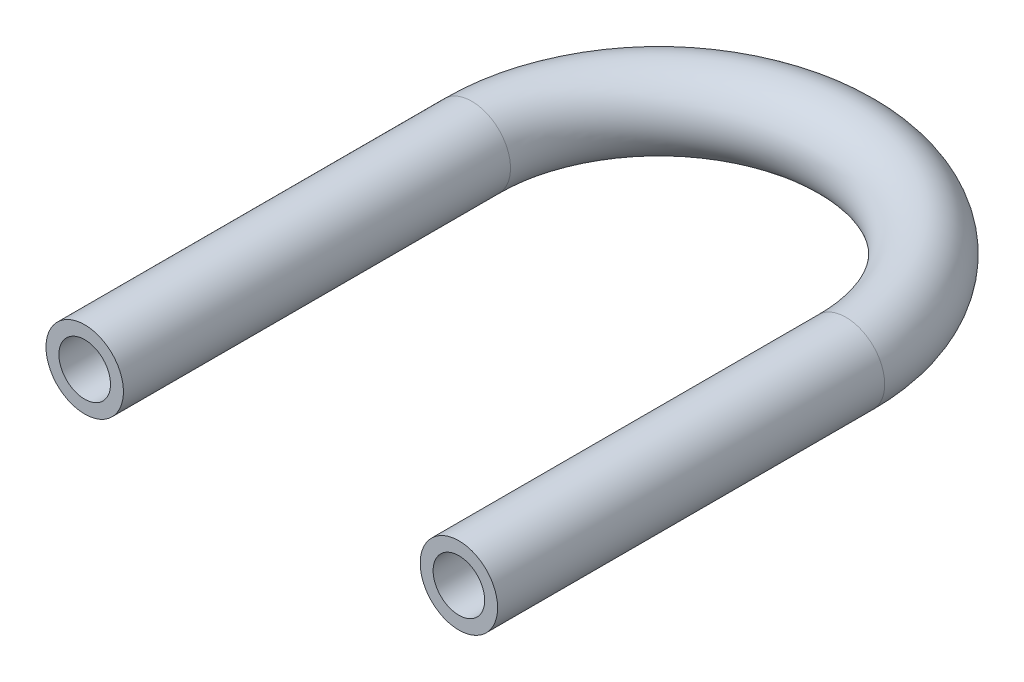
SolidWorks part; units mm, degrees
ref_plane "Front Plane" through (0, 0, 0) normal (0, 0, 1) x (1, 0, 0)
ref_plane "Top Plane" through (0, 0, 0) normal (0, 1, 0) x (1, 0, 0)
ref_plane "Right Plane" through (0, 0, 0) normal (1, 0, 0) x (0, 0, -1)
sketch "Sketch1" plane through (0, 0, 0) normal (0, 1, 0) x (1, 0, 0)
  line L0 (-14.5, 0) -> (-14.5, -30)
  line L1 (14.5, 0) -> (14.5, -30)
  arc A0 (-14.5, 0) -> (14.5, 0) centre (0, 0) cw
  dimension "D1" = 14.5
  dimension "D2" = 30
ref_plane "Plane1" through (-14.5, 0, 30) normal (0, 0, -1) x (-1, 0, 0)
sketch "Sketch2" plane through (-14.5, 0, 30) normal (0, 0, -1) x (-1, 0, 0)
  circle A0 centre (0, 0) radius 3
  circle A1 centre (0, 0) radius 2
  dimension "D1" = 6
  dimension "D2" = 4
sweep "Sweep1" add profiles "Sketch2" path "Sketch1"
